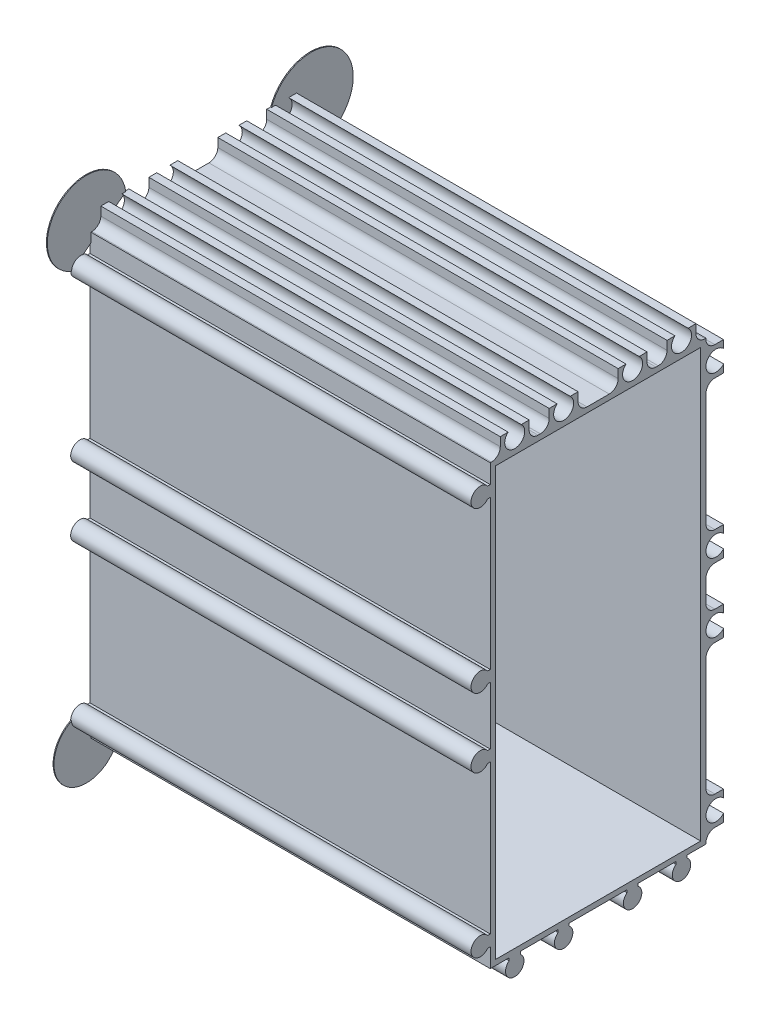
SolidWorks part; units mm, degrees
ref_plane "Спереди" through (0, 0, 0) normal (0, 0, 1) x (1, 0, 0)
ref_plane "Сверху" through (0, 0, 0) normal (0, 1, 0) x (1, 0, 0)
ref_plane "Справа" through (0, 0, 0) normal (1, 0, 0) x (0, 0, -1)
ref_plane "Плоскость4" through (90, 0, 0) normal (1, 0, 0) x (0, 0, -1)
sketch "Эскиз1" plane through (90, 0, 0) normal (1, 0, 0) x (0, 0, -1)
  line L0 (6.75, 225.9062) -> (6.75, 320.75)
  line L1 (6.75, 320.75) -> (-38.0938, 320.75)
  line L2 (-38.0938, 318.25) -> (-37.5, 318.25)
  line L3 (-37.5, 318.25) -> (-37.5, 284.75)
  line L4 (-37.5, 284.75) -> (-38.0938, 284.75)
  line L5 (-38.0938, 282.25) -> (-37.5, 282.25)
  line L6 (-37.5, 282.25) -> (-37.5, 269.25)
  line L7 (-37.5, 269.25) -> (-38.0938, 269.25)
  line L8 (-38.0938, 266.75) -> (-37.5, 266.75)
  line L9 (-37.5, 266.75) -> (-37.5, 233.25)
  line L10 (-37.5, 233.25) -> (-38.0938, 233.25)
  line L11 (-38.0938, 230.75) -> (-37.5, 230.75)
  line L12 (-37.5, 230.75) -> (-37.5, 226.5)
  line L13 (-37.5, 226.5) -> (-33.25, 226.5)
  line L14 (-33.25, 226.5) -> (-33.25, 225.9062)
  line L15 (-30.75, 225.9062) -> (-30.75, 226.5)
  line L16 (-30.75, 226.5) -> (-22.25, 226.5)
  line L17 (-22.25, 226.5) -> (-22.25, 225.9062)
  line L18 (-19.75, 225.9062) -> (-19.75, 226.5)
  line L19 (-19.75, 226.5) -> (-6.75, 226.5)
  line L20 (-6.75, 226.5) -> (-6.75, 225.9062)
  line L21 (-4.25, 225.9062) -> (-4.25, 226.5)
  line L22 (-4.25, 226.5) -> (4.25, 226.5)
  line L23 (4.25, 226.5) -> (4.25, 225.9062)
  arc A0 (-38.0938, 320.75) -> (-38.0938, 318.25) centre (-39.75, 319.5) ccw
  arc A1 (-38.0938, 284.75) -> (-38.0938, 282.25) centre (-39.75, 283.5) ccw
  arc A2 (-38.0938, 269.25) -> (-38.0938, 266.75) centre (-39.75, 268) ccw
  arc A3 (-38.0938, 233.25) -> (-38.0938, 230.75) centre (-39.75, 232) ccw
  arc A4 (-33.25, 225.9062) -> (-30.75, 225.9062) centre (-32, 224.25) ccw
  arc A5 (-22.25, 225.9062) -> (-19.75, 225.9062) centre (-21, 224.25) ccw
  arc A6 (-6.75, 225.9062) -> (-4.25, 225.9062) centre (-5.5, 224.25) ccw
  arc A7 (4.25, 225.9062) -> (6.75, 225.9062) centre (5.5, 224.25) ccw
extrude "Бобышка-Вытянуть1" add sketch "Эскиз1" against normal blind 90
sketch "Эскиз2" plane through (0, 320.75, 0) normal (0, 1, 0) x (-1, 0, 0)
  line L0 (-90, -6.75) -> (-90, 37.5)
  line L1 (-90, 37.5) -> (0, 37.5)
  line L2 (0, 37.5) -> (0, -6.75)
  line L3 (0, -6.75) -> (-90, -6.75)
extrude "Бобышка-Вытянуть2" add sketch "Эскиз2" along normal blind 8.2
sketch "Эскиз3" plane through (0, 0, -6.75) normal (0, 0, -1) x (-1, 0, 0)
  line L0 (-90, 226.5) -> (-90, 328.95)
  line L1 (-90, 328.95) -> (0, 328.95)
  line L2 (0, 328.95) -> (0, 226.5)
  line L3 (0, 226.5) -> (-90, 226.5)
extrude "Бобышка-Вытянуть3" add sketch "Эскиз3" along normal blind 8.2
sketch "Эскиз4" plane through (0, 0, 0) normal (-1, 0, 0) x (0, 0, 1)
  line L0 (24.25, 328.95) -> (24.25, 325)
  line L1 (24.25, 325) -> (28.75, 325)
  line L2 (28.75, 325) -> (28.75, 328.95)
  line L3 (28.75, 328.95) -> (24.25, 328.95)
extrude "Вырез-Вытянуть1" cut sketch "Эскиз4" against normal through all
sketch "Эскиз5" plane through (0, 0, 0) normal (-1, 0, 0) x (0, 0, 1)
  line L0 (37.5, 328.95) -> (35.25, 328.95)
  line L1 (35.25, 328.95) -> (35.25, 325)
  line L2 (35.25, 325) -> (37.5, 325)
  line L3 (37.5, 325) -> (37.5, 328.95)
extrude "Вырез-Вытянуть2" cut sketch "Эскиз5" against normal through all
sketch "Эскиз6" plane through (0, 0, 0) normal (-1, 0, 0) x (0, 0, 1)
  line L0 (-14.95, 226.5) -> (-11, 226.5)
  line L1 (-11, 226.5) -> (-11, 228.75)
  line L2 (-11, 228.75) -> (-14.95, 228.75)
  line L3 (-14.95, 228.75) -> (-14.95, 226.5)
extrude "Вырез-Вытянуть3" cut sketch "Эскиз6" against normal through all
sketch "Эскиз7" plane through (0, 0, 0) normal (-1, 0, 0) x (0, 0, 1)
  line L0 (-14.95, 235.25) -> (-11, 235.25)
  line L1 (-11, 235.25) -> (-11, 264.75)
  line L2 (-11, 264.75) -> (-14.95, 264.75)
  line L3 (-14.95, 264.75) -> (-14.95, 235.25)
extrude "Вырез-Вытянуть4" cut sketch "Эскиз7" against normal through all
sketch "Эскиз8" plane through (0, 0, 0) normal (-1, 0, 0) x (0, 0, 1)
  line L0 (-14.95, 271.25) -> (-11, 271.25)
  line L1 (-11, 271.25) -> (-11, 280.25)
  line L2 (-11, 280.25) -> (-14.95, 280.25)
  line L3 (-14.95, 280.25) -> (-14.95, 271.25)
extrude "Вырез-Вытянуть5" cut sketch "Эскиз8" against normal through all
sketch "Эскиз9" plane through (0, 0, 0) normal (-1, 0, 0) x (0, 0, 1)
  line L0 (-14.95, 286.75) -> (-11, 286.75)
  line L1 (-11, 286.75) -> (-11, 316.25)
  line L2 (-11, 316.25) -> (-14.95, 316.25)
  line L3 (-14.95, 316.25) -> (-14.95, 286.75)
extrude "Вырез-Вытянуть6" cut sketch "Эскиз9" against normal through all
sketch "Эскиз10" plane through (0, 0, 0) normal (-1, 0, 0) x (0, 0, 1)
  line L0 (-14.95, 328.95) -> (-14.95, 322.75)
  line L1 (-14.95, 322.75) -> (-11, 322.75)
  line L2 (-11, 322.75) -> (-11, 328.95)
  line L3 (-11, 328.95) -> (-14.95, 328.95)
extrude "Вырез-Вытянуть7" cut sketch "Эскиз10" against normal through all
sketch "Эскиз11" plane through (0, 0, 0) normal (-1, 0, 0) x (0, 0, 1)
  line L0 (-11, 328.95) -> (-11, 325)
  line L1 (-11, 325) -> (-8.75, 325)
  line L2 (-8.75, 325) -> (-8.75, 328.95)
  line L3 (-8.75, 328.95) -> (-11, 328.95)
extrude "Вырез-Вытянуть8" cut sketch "Эскиз11" against normal through all
sketch "Эскиз12" plane through (0, 0, 0) normal (-1, 0, 0) x (0, 0, 1)
  line L0 (-2.25, 328.95) -> (-2.25, 325)
  line L1 (-2.25, 325) -> (2.25, 325)
  line L2 (2.25, 325) -> (2.25, 328.95)
  line L3 (2.25, 328.95) -> (-2.25, 328.95)
extrude "Вырез-Вытянуть9" cut sketch "Эскиз12" against normal through all
sketch "Эскиз13" plane through (0, 0, 0) normal (-1, 0, 0) x (0, 0, 1)
  line L0 (8.75, 328.95) -> (8.75, 325)
  line L1 (8.75, 325) -> (17.75, 325)
  line L2 (17.75, 325) -> (17.75, 328.95)
  line L3 (17.75, 328.95) -> (8.75, 328.95)
extrude "Вырез-Вытянуть10" cut sketch "Эскиз13" against normal through all
sketch "Эскиз14" plane through (90, 0, 0) normal (1, 0, 0) x (0, 0, -1)
  line L0 (9.8, 323.8) -> (-36.3, 323.8)
  line L1 (-36.3, 323.8) -> (-36.3, 227.7)
  line L2 (-36.3, 227.7) -> (9.8, 227.7)
  line L3 (9.8, 227.7) -> (9.8, 323.8)
  line L4 (-37.5, 318.25) -> (-37.5, 284.75) construction
  line L5 (-8.75, 325) -> (-17.75, 325) construction
  line L6 (11, 286.75) -> (11, 316.25) construction
  line L7 (-19.75, 226.5) -> (-6.75, 226.5) construction
  dimension "D1" = 1.2
  dimension "D2" = 1.2
  dimension "D3" = 1.2
  dimension "D4" = 1.2
extrude "Вырез-Вытянуть11" cut sketch "Эскиз14" against normal blind 86.6
hole_wizard "Диаметр отверстия Ø2.5 (2.5)1" positions "Эскиз16" profile "Эскиз15" hole size "Ø2.5" standard "Ansi Metric"
sketch "Эскиз16" plane through (90, 0, 0) normal (1, 0, 0) x (0, 0, -1)
  point P0 (-39.75, 232)
  point P1 (-21, 224.25)
  point P2 (-39.75, 283.5)
  point P3 (-5.5, 224.25)
  point P4 (5.5, 224.25)
  point P5 (-39.75, 319.5)
  point P6 (-39.75, 268)
  point P7 (-32, 224.25)
sketch "Эскиз15" plane through (90, 232, 39.75) normal (0, 1, 0) x (0, 0, -1)
  line L0 (0, 0) -> (0, 90)
  line L1 (0, 90) -> (1.25, 90)
  line L2 (1.25, 90) -> (1.25, 0)
  line L5 (1.25, 0) -> (0, 0)
  line L11 (0, -6.35) -> (0, 107.95) construction
  dimension "Диаметр сквозного отверстия" = 2.5
  dimension "Глубина сквозного отверстия" = 90
hole_wizard "Диаметр отверстия Ø4.5 (4.5)1" positions "Эскиз18" profile "Эскиз17" hole size "Ø4.5" standard "Ansi Metric"
sketch "Эскиз18" plane through (0, 0, 0) normal (-1, 0, 0) x (0, 0, 1)
  point P0 (21, 327.25)
  point P1 (32, 327.25)
  point P2 (-13.25, 232)
  point P3 (-13.25, 268)
  point P4 (-13.25, 283.5)
  point P5 (-13.25, 319.5)
  point P6 (-5.5, 327.25)
  point P7 (5.5, 327.25)
sketch "Эскиз17" plane through (0, 327.25, 21) normal (0, 1, 0) x (0, 0, 1)
  line L0 (0, 0) -> (0, 90)
  line L1 (0, 90) -> (2.25, 90)
  line L2 (2.25, 90) -> (2.25, 0)
  line L5 (2.25, 0) -> (0, 0)
  line L11 (0, -6.35) -> (0, 107.95) construction
  dimension "Диаметр сквозного отверстия" = 4.5
  dimension "Глубина сквозного отверстия" = 90
hole_wizard "Диаметр отверстия Ø8.3 (8.3)1" [suppressed] positions "Эскиз20" profile "Эскиз19" hole size "Ø8.3" standard "Ansi Metric"
sketch "Эскиз20" plane through (0, 0, 0) normal (-1, 0, 0) x (0, 0, 1)
  point P0 (13.25, 275.75)
sketch "Эскиз19" plane through (0, 275.75, 13.25) normal (0, 1, 0) x (0, 0, 1)
  line L0 (0, 0) -> (0, 3.2)
  line L1 (0, 3.2) -> (4.15, 3.2)
  line L2 (4.15, 3.2) -> (4.15, 0)
  line L5 (4.15, 0) -> (0, 0)
  line L10 (0, 3.2) -> (-4.15, 3.2) construction
  line L11 (0, -6.35) -> (0, 107.95) construction
  dimension "Диаметр отверстия" = 8.3
  dimension "Глубина отверстия" = 3.2
  dimension "Угол заточки сверла" = 180
sketch "Эскиз21" [suppressed] plane through (0, 0, 0) normal (-1, 0, 0) x (0, 0, 1)
  circle A0 centre (13.25, 275.75) radius 4.15
extrude "Вырез-Вытянуть12" [suppressed] cut sketch "Эскиз21" against normal blind 10
sketch "Эскиз22" plane through (90, 0, 0) normal (1, 0, 0) x (0, 0, -1)
  circle A0 centre (-39.75, 319.5) radius 1.6316
  circle A1 centre (-39.75, 283.5) radius 1.5194
  circle A2 centre (-39.75, 268) radius 1.4876
  circle A3 centre (-39.75, 232) radius 1.5817
  circle A4 centre (-32, 224.25) radius 1.4878
  circle A5 centre (-21, 224.25) radius 1.426
  circle A6 centre (-5.5, 224.25) radius 1.6281
  circle A7 centre (5.5, 224.25) radius 1.5237
extrude "Бобышка-Вытянуть4" add sketch "Эскиз22" against normal blind 90
fillet "Скругление1" [suppressed] radius 2
fillet "Скругление2" [suppressed] radius 2
fillet "Скругление3" [suppressed] radius 2
fillet "Скругление4" [suppressed] radius 2
fillet "Скругление5" radius 2 1 edges at (45, 325, 35.25)
fillet "Скругление6" radius 2 1 edges at (45, 325, 28.75)
fillet "Скругление7" radius 2 1 edges at (45, 325, 24.25)
fillet "Скругление8" radius 2 1 edges at (45, 325, 17.75)
fillet "Скругление9" radius 2 1 edges at (45, 325, 8.75)
fillet "Скругление10" radius 2 1 edges at (45, 325, 2.25)
fillet "Скругление11" radius 2 1 edges at (45, 325, -2.25)
fillet "Скругление12" radius 2 1 edges at (45, 325, -8.75)
fillet "Скругление13" radius 2 1 edges at (45, 322.75, -11)
fillet "Скругление14" radius 2 1 edges at (45, 316.25, -11)
fillet "Скругление15" radius 2 1 edges at (45, 286.75, -11)
fillet "Скругление16" radius 2 1 edges at (45, 280.25, -11)
fillet "Скругление17" radius 2 1 edges at (45, 271.25, -11)
fillet "Скругление18" radius 2 1 edges at (45, 264.75, -11)
fillet "Скругление19" radius 2 1 edges at (45, 235.25, -11)
fillet "Скругление20" radius 2 1 edges at (45, 228.75, -11)
sketch "Эскиз23" plane through (0, 0, 0) normal (-1, 0, 0) x (0, 0, 1)
  line L0 (-4.0261, 328.95) -> (-2.25, 328.95) construction
  line L1 (-14.95, 316.25) -> (-14.95, 318.0261) construction
  line L2 (28.75, 328.95) -> (30.5261, 328.95) construction
  line L3 (-14.95, 316.8156) -> (-3.138, 328.95)
  line L4 (41.825, 319.5) -> (29.638, 328.95)
  line L5 (-14.95, 233.4739) -> (-14.95, 235.25) construction
  line L6 (-14.95, 234.362) -> (-5.5, 222.175)
  line L7 (32, 222.175) -> (41.825, 232)
  arc A0 (-3.138, 328.95) -> (-14.95, 316.8156) centre (-12.0452, 325.8043) ccw
  arc A1 (41.825, 319.5) -> (29.638, 328.95) centre (38.4167, 327.6879) ccw
  arc A2 (38.0938, 318.25) -> (38.0938, 320.75) centre (39.75, 319.5) ccw construction
  arc A3 (-5.5, 222.175) -> (-14.95, 234.362) centre (-12.6196, 226.4117) cw
  arc A4 (-6.75, 225.9062) -> (-4.25, 225.9062) centre (-5.5, 224.25) ccw construction
  arc A5 (41.825, 232) -> (32, 222.175) centre (38.485, 225.515) cw
  arc A6 (38.0938, 230.75) -> (38.0938, 233.25) centre (39.75, 232) ccw construction
  arc A7 (30.75, 225.9062) -> (33.25, 225.9062) centre (32, 224.25) ccw construction
extrude "Бобышка-Вытянуть6" add sketch "Эскиз23" against normal blind 0.2
equation "\"D2@Эскиз14\"=\"D1@Эскиз14\""
equation "\"D3@Эскиз14\"=\"D1@Эскиз14\""
equation "\"D4@Эскиз14\"=\"D1@Эскиз14\""
